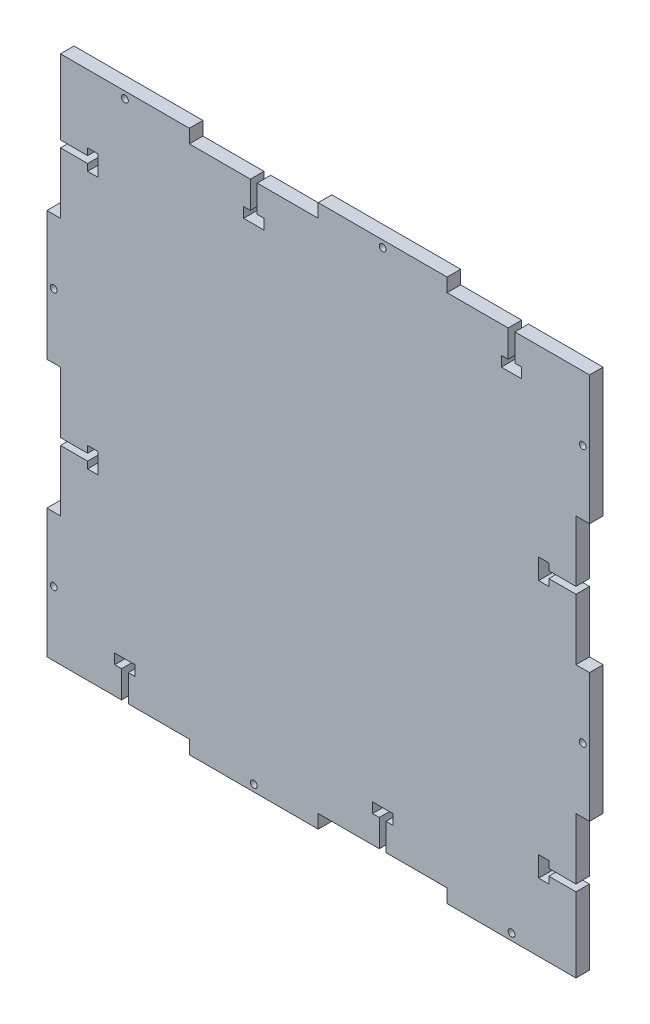
SolidWorks part; units mm, degrees
ref_plane "Front Plane" through (0, 0, 0) normal (0, 0, 1) x (1, 0, 0)
ref_plane "Top Plane" through (0, 0, 0) normal (0, 1, 0) x (1, 0, 0)
ref_plane "Right Plane" through (0, 0, 0) normal (1, 0, 0) x (0, 0, -1)
sketch "Sketch1" plane through (0, 0, 0) normal (0, 0, 1) x (1, 0, 0)
  line L0 (-60.325, 60.325) -> (-60.325, 63.5)
  line L13 (63.5, -63.5) -> (-63.5, -63.5) construction
  line L15 (63.5, -63.5) -> (63.5, 63.5) construction
  line L16 (63.5, 63.5) -> (-63.5, 63.5) construction
  line L17 (-63.5, -63.5) -> (-63.5, 63.5) construction
  line L18 (63.5, -63.5) -> (-63.5, 63.5) construction
  line L19 (63.5, 63.5) -> (-63.5, -63.5) construction
  line L20 (-60.325, 63.5) -> (-30.1625, 63.5)
  line L21 (-30.1625, 63.5) -> (-30.1625, 60.325)
  line L22 (-30.1625, 60.325) -> (0, 60.325)
  line L23 (0, 60.325) -> (0, 63.5)
  line L24 (0, 63.5) -> (30.1625, 63.5)
  line L25 (30.1625, 63.5) -> (30.1625, 60.325)
  line L26 (30.1625, 60.325) -> (60.325, 60.325)
  line L27 (60.325, 60.325) -> (63.5, 60.325)
  line L28 (63.5, 60.325) -> (63.5, 30.1625)
  line L29 (63.5, 30.1625) -> (60.325, 30.1625)
  line L30 (60.325, 30.1625) -> (60.325, 0)
  line L31 (60.325, 0) -> (63.5, 0)
  line L32 (63.5, 0) -> (63.5, -30.1625)
  line L33 (63.5, -30.1625) -> (60.325, -30.1625)
  line L34 (60.325, -30.1625) -> (60.325, -60.325)
  line L35 (60.325, -60.325) -> (60.325, -63.5)
  line L36 (60.325, -63.5) -> (30.1625, -63.5)
  line L37 (30.1625, -63.5) -> (30.1625, -60.325)
  line L38 (30.1625, -60.325) -> (0, -60.325)
  line L39 (0, -60.325) -> (0, -63.5)
  line L40 (0, -63.5) -> (-30.1625, -63.5)
  line L41 (-30.1625, -63.5) -> (-30.1625, -60.325)
  line L42 (-30.1625, -60.325) -> (-60.325, -60.325)
  line L43 (-60.325, -60.325) -> (-63.5, -60.325)
  line L44 (-63.5, -60.325) -> (-63.5, -30.1625)
  line L45 (-63.5, -30.1625) -> (-60.325, -30.1625)
  line L46 (-60.325, -30.1625) -> (-60.325, 0)
  line L47 (-60.325, 0) -> (-63.5, 0)
  line L48 (-63.5, 0) -> (-63.5, 30.1625)
  line L49 (-63.5, 30.1625) -> (-60.325, 30.1625)
  line L50 (-60.325, 30.1625) -> (-60.325, 60.325)
  point P0 (0, 0)
  point P45 (0, 0)
  dimension "D1" = 127
  dimension "D2" = 30.1625
  dimension "D3" = 3.175
  dimension "D5" = 3.175
  dimension "D4" = 2
  dimension "D6" = 4
extrude "Boss-Extrude1" add sketch "Sketch1" along normal blind 3.175 contours L20 L21 L22 L23 L24 L25 L26 L27 L28 L29 L30 L31 L32 L33 L34 L35 L36 L37 L38 L39 L40 L41 L42 L43 L44 L45 L46 L47 L48 L49 L50 L0
sketch "Sketch2" plane through (0, 0, 3.175) normal (0, 0, 1) x (1, 0, 0)
  line L0 (-30.1625, 60.325) -> (0, 60.325) construction
  line L1 (-14.2875, 67.8656) -> (-15.875, 67.8656)
  line L2 (-14.2875, 67.8656) -> (-14.2875, 52.7844)
  line L3 (-14.2875, 52.7844) -> (-15.875, 52.7844)
  line L4 (-15.875, 67.8656) -> (-15.875, 52.7844)
  line L5 (-14.2875, 67.8656) -> (-15.875, 52.7844) construction
  line L6 (-14.2875, 52.7844) -> (-15.875, 67.8656) construction
  line L7 (-60.325, 63.5) -> (-30.1625, 63.5) construction
  line L8 (-17.4625, 51.5938) -> (-12.7, 51.5938)
  line L9 (-17.4625, 51.5938) -> (-17.4625, 53.975)
  line L10 (-17.4625, 53.975) -> (-12.7, 53.975)
  line L11 (-12.7, 51.5938) -> (-12.7, 53.975)
  line L12 (-17.4625, 51.5938) -> (-12.7, 53.975) construction
  line L13 (-17.4625, 53.975) -> (-12.7, 51.5938) construction
  line L14 (-30.1625, 63.5) -> (-30.1625, 60.325) construction
  line L15 (46.0375, 67.8656) -> (46.0375, 52.7844)
  line L16 (46.0375, 67.8656) -> (44.45, 67.8656)
  line L17 (44.45, 67.8656) -> (44.45, 52.7844)
  line L18 (46.0375, 52.7844) -> (44.45, 52.7844)
  line L19 (42.8625, 51.5938) -> (42.8625, 53.975)
  line L20 (42.8625, 51.5938) -> (47.625, 51.5938)
  line L21 (47.625, 51.5938) -> (47.625, 53.975)
  line L22 (42.8625, 53.975) -> (47.625, 53.975)
  line L23 (67.8656, 14.2875) -> (52.7844, 14.2875)
  line L24 (67.8656, 14.2875) -> (67.8656, 15.875)
  line L25 (67.8656, 15.875) -> (52.7844, 15.875)
  line L26 (52.7844, 14.2875) -> (52.7844, 15.875)
  line L27 (51.5938, 17.4625) -> (53.975, 17.4625)
  line L28 (51.5938, 17.4625) -> (51.5938, 12.7)
  line L29 (51.5938, 12.7) -> (53.975, 12.7)
  line L30 (53.975, 17.4625) -> (53.975, 12.7)
  line L31 (67.8656, -46.0375) -> (52.7844, -46.0375)
  line L32 (52.7844, -46.0375) -> (52.7844, -44.45)
  line L33 (67.8656, -44.45) -> (52.7844, -44.45)
  line L34 (67.8656, -46.0375) -> (67.8656, -44.45)
  line L35 (51.5938, -42.8625) -> (53.975, -42.8625)
  line L36 (53.975, -42.8625) -> (53.975, -47.625)
  line L37 (51.5938, -47.625) -> (53.975, -47.625)
  line L38 (51.5938, -42.8625) -> (51.5938, -47.625)
  line L39 (14.2875, -67.8656) -> (14.2875, -52.7844)
  line L40 (14.2875, -67.8656) -> (15.875, -67.8656)
  line L41 (15.875, -67.8656) -> (15.875, -52.7844)
  line L42 (14.2875, -52.7844) -> (15.875, -52.7844)
  line L43 (17.4625, -51.5937) -> (17.4625, -53.975)
  line L44 (17.4625, -51.5937) -> (12.7, -51.5937)
  line L45 (12.7, -51.5937) -> (12.7, -53.975)
  line L46 (17.4625, -53.975) -> (12.7, -53.975)
  line L47 (-46.0375, -67.8656) -> (-46.0375, -52.7844)
  line L48 (-46.0375, -52.7844) -> (-44.45, -52.7844)
  line L49 (-44.45, -67.8656) -> (-44.45, -52.7844)
  line L50 (-46.0375, -67.8656) -> (-44.45, -67.8656)
  line L51 (-42.8625, -51.5937) -> (-42.8625, -53.975)
  line L52 (-42.8625, -53.975) -> (-47.625, -53.975)
  line L53 (-47.625, -51.5937) -> (-47.625, -53.975)
  line L54 (-42.8625, -51.5937) -> (-47.625, -51.5937)
  line L55 (-67.8656, -14.2875) -> (-52.7844, -14.2875)
  line L56 (-67.8656, -14.2875) -> (-67.8656, -15.875)
  line L57 (-67.8656, -15.875) -> (-52.7844, -15.875)
  line L58 (-52.7844, -14.2875) -> (-52.7844, -15.875)
  line L59 (-51.5937, -17.4625) -> (-53.975, -17.4625)
  line L60 (-51.5937, -17.4625) -> (-51.5937, -12.7)
  line L61 (-51.5937, -12.7) -> (-53.975, -12.7)
  line L62 (-53.975, -17.4625) -> (-53.975, -12.7)
  line L63 (-67.8656, 46.0375) -> (-52.7844, 46.0375)
  line L64 (-52.7844, 46.0375) -> (-52.7844, 44.45)
  line L65 (-67.8656, 44.45) -> (-52.7844, 44.45)
  line L66 (-67.8656, 46.0375) -> (-67.8656, 44.45)
  line L67 (-51.5937, 42.8625) -> (-53.975, 42.8625)
  line L68 (-53.975, 42.8625) -> (-53.975, 47.625)
  line L69 (-51.5937, 47.625) -> (-53.975, 47.625)
  line L70 (-51.5937, 42.8625) -> (-51.5937, 47.625)
  circle A0 centre (-45.2437, 61.9125) radius 0.7937
  circle A1 centre (15.0813, 61.9125) radius 0.7937
  circle A2 centre (61.9125, 45.2438) radius 0.7938
  circle A3 centre (61.9125, -15.0812) radius 0.7938
  circle A4 centre (45.2438, -61.9125) radius 0.7938
  circle A5 centre (-15.0812, -61.9125) radius 0.7938
  circle A6 centre (-61.9125, -45.2438) radius 0.7938
  circle A7 centre (-61.9125, 15.0812) radius 0.7938
  point P0 (-15.0812, 60.325)
  point P7 (-15.0812, 52.7844)
  point P17 (-45.2437, 63.5)
  point P20 (-30.1625, 61.9125)
  point P93 (0, 0)
  dimension "D4" = 1.5875
  dimension "D1" = 2.3812
  dimension "D2" = 4.7625
  dimension "D3" = 1.5875
  dimension "D5" = 6.35
  dimension "D6" = 2
  dimension "D7" = 4
extrude "Cut-Extrude1" cut sketch "Sketch2" against normal through all contours L67 L70 L69 L68 L63 L64 L65 | A0 | L8 L11 L10 L2 L3 L4 L9 | A1 | L17 L22 L15 L23 | L22 L17 L18 L15 | L22 L19 L20 L21 L15 L18 L17 | A2 | L29 L30 L27 L28 | A3 | L33 L32 L31 L34 | L37 L36 L35 L38 | A4 | L41 L42 L39 L40 | L46 L45 L44 L43 | A5 | L52 L53 L54 L51 | L49 L48 L47 L50 | A6 | L57 L58 L55 L56 | L59 L62 L61 L60 | A7
equation "\"Notches\"= 2'Number of fitted notches per side"
equation "\"Panel_Thickness\"= .125in'Thickness of panel"
equation "\"Panel_Length\"= 5in'Length of side of panel"
equation "\"D1@Sketch1\"=\"Panel_Length\""
equation "\"D2@Sketch1\"=((\"Panel_Length\"-(\"Panel_Thickness\"*2))/2)/(\"Notches\")"
equation "\"D3@Sketch1\"=\"Panel_Thickness\""
equation "\"D5@Sketch1\"=\"Panel_Thickness\""
equation "\"D1@Boss-Extrude1\"=\"Panel_Thickness\""
